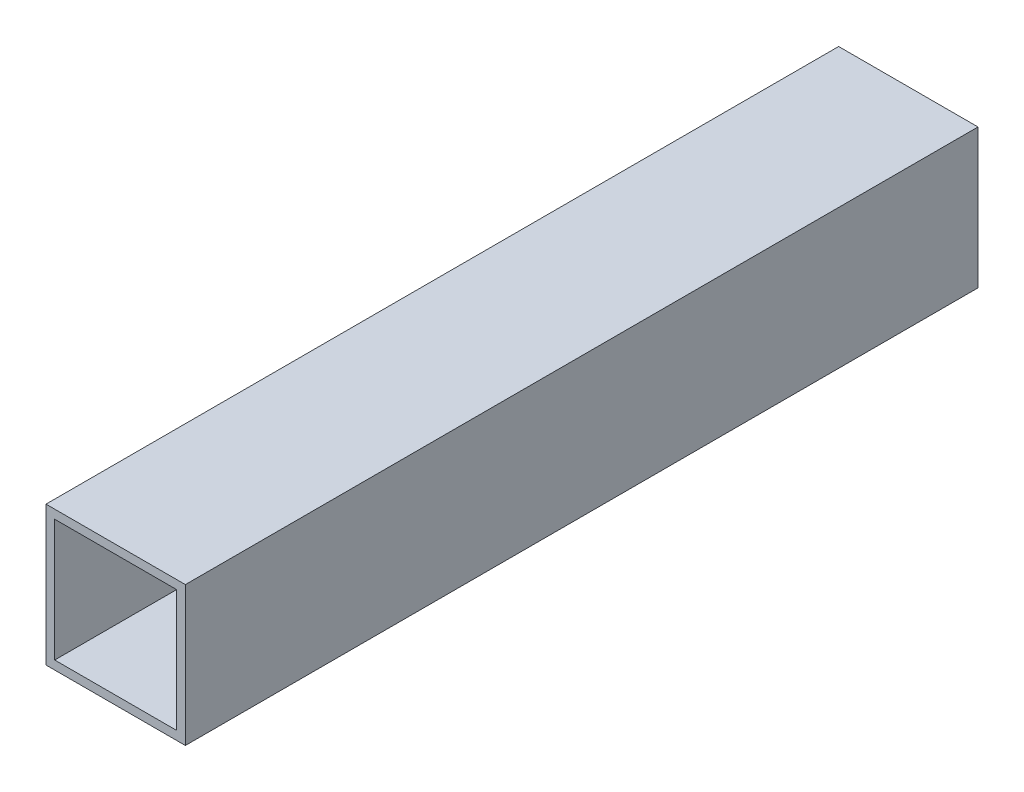
SolidWorks part; units mm, degrees
material "6061-T6 (SS)"
ref_plane "Front Plane" through (0, 0, 0) normal (0, 0, 1) x (1, 0, 0)
ref_plane "Top Plane" through (0, 0, 0) normal (0, 1, 0) x (1, 0, 0)
ref_plane "Right Plane" through (0, 0, 0) normal (1, 0, 0) x (0, 0, -1)
sketch "Sketch1" plane through (0, 0, 0) normal (0, 0, 1) x (1, 0, 0)
  line L0 (-11.1125, 11.1125) -> (11.1125, 11.1125)
  line L2 (-12.7, 12.7) -> (12.7, 12.7)
  line L3 (-12.7, 12.7) -> (-12.7, -12.7)
  line L4 (-12.7, -12.7) -> (12.7, -12.7)
  line L5 (12.7, 12.7) -> (12.7, -12.7)
  line L10 (11.1125, 11.1125) -> (11.1125, -11.1125)
  line L11 (-11.1125, -11.1125) -> (11.1125, -11.1125)
  line L12 (-11.1125, 11.1125) -> (-11.1125, -11.1125)
  point P12 (0, 12.7)
  point P14 (12.7, 0)
  dimension "Wall Thickness" = 1.5875
  dimension "Outside Width" = 25.4
  dimension "Outside Height" = 25.4
  dimension "Inside Height" = 22.225
  dimension "Inside Width" = 22.225
sketch "Sketch2" plane through (0, 0, 0) normal (1, 0, 0) x (0, 0, -1)
  line L0 (76.2, 0) -> (-76.2, 0)
  point P4 (0, 0)
  point P7 (-76.2, 0)
  point P10 (76.2, 0)
  dimension "Length" = 152.4
sketch "Sketch3" plane through (0, 0, 0) normal (0, 0, 1) x (1, 0, 0)
  line L21 (12.7, 12.7) -> (-12.7, 12.7)
  line L22 (12.7, -12.7) -> (12.7, 12.7)
  line L23 (-12.7, -12.7) -> (12.7, -12.7)
  line L24 (-12.7, 12.7) -> (-12.7, -12.7)
  line L25 (12.7, 12.7) -> (-12.7, 12.7)
  line L26 (12.7, -12.7) -> (12.7, 12.7)
  line L27 (-12.7, -12.7) -> (12.7, -12.7)
  line L28 (-12.7, 12.7) -> (-12.7, -12.7)
  line L29 (11.1125, 11.1125) -> (-11.1125, 11.1125)
  line L30 (11.1125, -11.1125) -> (11.1125, 11.1125)
  line L31 (-11.1125, -11.1125) -> (11.1125, -11.1125)
  line L32 (-11.1125, 11.1125) -> (-11.1125, -11.1125)
  line L33 (11.1125, 11.1125) -> (-11.1125, 11.1125)
  line L34 (11.1125, -11.1125) -> (11.1125, 11.1125)
  line L35 (-11.1125, -11.1125) -> (11.1125, -11.1125)
  line L36 (-11.1125, 11.1125) -> (-11.1125, -11.1125)
  dimension "D1" = 0
  dimension "D2" = 0
extrude "Boss-Extrude1" add sketch "Sketch3" along normal up to vertex (76.2 mm away) and the other way up to vertex (76.2 mm away) up to point (0, 0, 76.2) other way up to point (0, 0, -76.2)
sketch "Drawing Reference" plane through (0, 0, 0) normal (1, 0, 0) x (0, 0, -1)
  line L0 (-76.2, 0) -> (76.2, 0) construction
  line L1 (0, -12.7) -> (0, 12.7) construction
  line L2 (-76.2, -12.7) -> (76.2, -12.7) construction
  line L5 (-76.2, 12.7) -> (76.2, 12.7) construction
  point P7 (-57.912, 0)
  point P8 (57.912, 0)
  dimension "D1" = 18.288
sketch "Sketch4" plane through (0, 0, -76.2) normal (0, 0, -1) x (-1, 0, 0)
  line L4 (11.1125, 11.1125) -> (-11.1125, 11.1125)
  line L5 (11.1125, -11.1125) -> (11.1125, 11.1125)
  line L6 (-11.1125, -11.1125) -> (11.1125, -11.1125)
  line L7 (-11.1125, 11.1125) -> (-11.1125, -11.1125)
  line L8 (11.1125, 11.1125) -> (-11.1125, 11.1125)
  line L9 (11.1125, -11.1125) -> (11.1125, 11.1125)
  line L10 (-11.1125, -11.1125) -> (11.1125, -11.1125)
  line L11 (-11.1125, 11.1125) -> (-11.1125, -11.1125)
  line L12 (12.7, -12.7) -> (12.7, 12.7)
  line L13 (12.7, 12.7) -> (-12.7, 12.7)
  line L14 (-12.7, 12.7) -> (-12.7, -12.7)
  line L15 (-12.7, -12.7) -> (12.7, -12.7)
  line L16 (12.7, -12.7) -> (12.7, 12.7)
  line L17 (12.7, 12.7) -> (-12.7, 12.7)
  line L18 (-12.7, 12.7) -> (-12.7, -12.7)
  line L19 (-12.7, -12.7) -> (12.7, -12.7)
  point P2 (0, 0)
  dimension "D1" = 0
  dimension "D2" = 0
extrude "Cut-Extrude1" cut sketch "Sketch4" against normal offset from surface (7.9375 mm away) 144.4625 up to face at (0, 0, 76.2)
equation "\"D1@Drawing Reference\"=\"Outside Width@Sketch1\" * 0.72"
